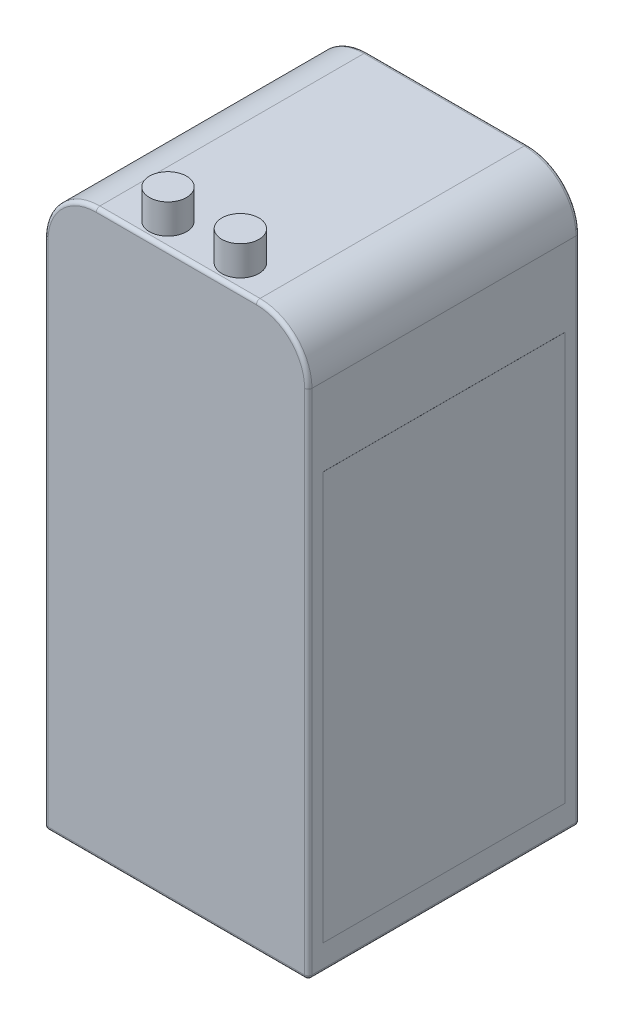
SolidWorks part; units mm, degrees
ref_plane "Front Plane" through (0, 0, 0) normal (0, 0, 1) x (1, 0, 0)
ref_plane "Top Plane" through (0, 0, 0) normal (0, 1, 0) x (1, 0, 0)
ref_plane "Right Plane" through (0, 0, 0) normal (1, 0, 0) x (0, 0, -1)
sketch "Sketch1" plane through (0, 0, 0) normal (0, 1, 0) x (1, 0, 0)
  line L1 (0, 0) -> (35.6, 0)
  line L2 (0, 0) -> (0, 36.6)
  line L3 (0, 36.6) -> (35.6, 36.6)
  line L4 (35.6, 0) -> (35.6, 36.6)
  dimension "D1" = 35.6
  dimension "D2" = 36.6
extrude "Boss-Extrude1" add sketch "Sketch1" along normal blind 76
sketch "Sketch2" plane through (0, 76, 0) normal (0, 1, 0) x (1, 0, 0)
  circle A0 centre (13.3548, 3.3233) radius 2.5
  circle A1 centre (23.1207, 3.3233) radius 2.5
  dimension "D1" = 5
  dimension "D2" = 5
extrude "Boss-Extrude2" add sketch "Sketch2" along normal blind 4 separate body
fillet "Fillet1" radius 7 2 edges at (0, 76, -18.3) (35.6, 76, -18.3)
fillet "Fillet2" radius 0.5 14 edges at (33.5497, 73.9497, 0) (35.6, 34.5, 0) (17.8, 0, 0) (0, 34.5, 0) (2.0503, 73.9497, 0) (17.8, 76, 0) (17.8, 0, -36.6) (35.6, 34.5, -36.6) (33.5497, 73.9497, -36.6) (17.8, 76, -36.6) (2.0503, 73.9497, -36.6) (0, 34.5, -36.6) (0, 0, -18.3) (35.6, 0, -18.3)
sketch "Sketch3" plane through (35.6, 0, 0) normal (1, 0, 0) x (0, 0, -1)
  line L0 (36.1, 0.5) -> (36.1, 69) construction
  line L1 (2, 58.5) -> (34.6, 58.5)
  line L2 (2, 58.5) -> (2, 3.5)
  line L3 (2, 3.5) -> (34.6, 3.5)
  line L4 (34.6, 58.5) -> (34.6, 3.5)
  line L5 (0.5, 69) -> (0.5, 0.5) construction
  line L6 (0.5, 0.5) -> (36.1, 0.5) construction
  dimension "D1" = 1.5
  dimension "D2" = 1.5
  dimension "D3" = 3
  dimension "D4" = 55
extrude "Boss-Extrude3" add sketch "Sketch3" along normal blind 0.01
